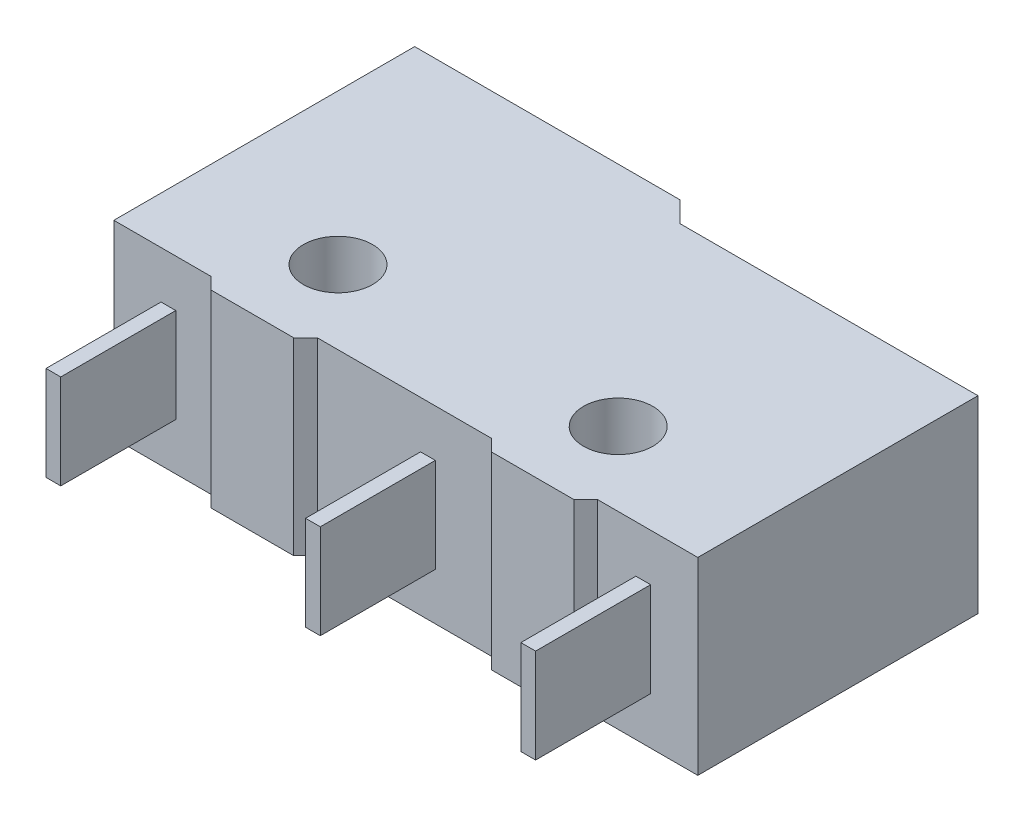
SolidWorks part; units mm, degrees
ref_plane "Front Plane" through (0, 0, 0) normal (0, 0, 1) x (1, 0, 0)
ref_plane "Top Plane" through (0, 0, 0) normal (0, 1, 0) x (1, 0, 0)
ref_plane "Right Plane" through (0, 0, 0) normal (1, 0, 0) x (0, 0, -1)
sketch "Sketch2" plane through (0, 0, 0) normal (0, 1, 0) x (1, 0, 0)
  line L0 (9.5, 0) -> (9.5, -2.5) construction
  line L1 (9.5, -2.5) -> (14.7, -2.5) construction
  line L2 (0, 0) -> (0, -2.5) construction
  line L3 (0, -2.5) -> (-5.1, -2.5) construction
  line L4 (0, 0) -> (0, -2.9) construction
  line L5 (0, -2.9) -> (-1.4, -2.9)
  line L6 (0, -2.9) -> (1.4, -2.9)
  line L7 (9.5, 0) -> (9.5, -2.9) construction
  line L8 (9.5, -2.9) -> (10.9, -2.9)
  line L9 (9.5, -2.9) -> (8.1, -2.9)
  line L10 (-1.4, -2.9) -> (-1.8, -2.5)
  line L11 (1.4, -2.9) -> (1.8, -2.5)
  line L12 (8.1, -2.9) -> (7.7, -2.5)
  line L13 (7.7, -2.5) -> (1.8, -2.5)
  line L14 (10.9, -2.9) -> (11.3, -2.5)
  line L15 (11.3, -2.5) -> (14.7, -2.5)
  line L16 (-1.8, -2.5) -> (-5.1, -2.5)
  line L17 (14.7, -2.5) -> (14.7, 7)
  line L18 (-5.1, -2.5) -> (-5.1, 7.7)
  line L19 (-5.1, 7.7) -> (3.9, 7.7)
  line L20 (3.9, 7.7) -> (4.6, 7)
  line L21 (4.6, 7) -> (14.7, 7)
  circle A0 centre (0, 0) radius 1.175
  circle A1 centre (9.5, 0) radius 1.175
  dimension "D1" = 2.35
  dimension "D2" = 2.35
  dimension "D3" = 9.5
  dimension "D4" = 5.2
  dimension "D5" = 2.5
  dimension "D6" = 2.5
  dimension "D7" = 5.1
  dimension "D8" = 2.9
  dimension "D9" = 1.4
  dimension "D10" = 1.4
  dimension "D11" = 1.4
  dimension "D12" = 1.4
  dimension "D13" = 2.9
  dimension "D14" = 135
  dimension "D15" = 135
  dimension "D16" = 135
  dimension "D17" = 135
  dimension "D18" = 9.5
  dimension "D19" = 10.2
  dimension "D20" = 9
  dimension "D21" = 10.1
extrude "Boss-Extrude1" add sketch "Sketch2" along normal blind 6.4
ref_plane "Plane1" through (0, 3.2, 0) normal (0, 1, 0) x (1, 0, 0)
sketch "Sketch3" plane through (0, 3.2, 0) normal (0, 1, 0) x (1, 0, 0)
  line L0 (3.9, 7.7) -> (3, 7.7) construction
  line L1 (3, 7.7) -> (1, 7.7)
  line L2 (2, 7.7) -> (2, 8.5382) construction
  line L3 (1, 7.7) -> (1, 7.954)
  line L4 (3, 7.7) -> (3, 7.954)
  spline S0 degree 2 poles (1, 7.954) (2, 9.1224) (3, 7.954) knots 0 0 0 1 1 1
  dimension "D1" = 2
  dimension "D2" = 0.9
  dimension "D3" = 0.8382
  dimension "D4" = 0.254
  dimension "D5" = 0.254
extrude "Boss-Extrude2" add sketch "Sketch3" along normal blind 1.6 and the other way blind 1.6
sketch "Sketch4" plane through (0, 3.2, 0) normal (0, 1, 0) x (1, 0, 0)
  line L0 (-5.1, -2.5) -> (-3.5, -2.5) construction
  line L1 (-3.5, -2.5) -> (-3, -2.5)
  line L2 (-3.5, -2.5) -> (-3.5, -6.4)
  line L3 (-3.5, -6.4) -> (-3, -6.4)
  line L4 (-3, -2.5) -> (-3, -6.4)
  line L5 (5.3, -2.5) -> (5.8, -2.5)
  line L6 (5.3, -2.5) -> (5.3, -6.4)
  line L7 (5.3, -6.4) -> (5.8, -6.4)
  line L8 (5.8, -2.5) -> (5.8, -6.4)
  line L9 (12.6, -2.5) -> (13.1, -2.5)
  line L10 (12.6, -2.5) -> (12.6, -6.4)
  line L11 (12.6, -6.4) -> (13.1, -6.4)
  line L12 (13.1, -2.5) -> (13.1, -6.4)
  line L13 (1.8, -2.5) -> (5.3, -2.5) construction
  line L14 (12.6, -2.5) -> (11.3, -2.5) construction
  point P20 (11.3, -2.5)
  dimension "D1" = 0.5
  dimension "D2" = 0.5
  dimension "D3" = 0.5
  dimension "D4" = 3.9
  dimension "D5" = 3.9
  dimension "D6" = 3.9
  dimension "D7" = 1.6
  dimension "D8" = 3.5
  dimension "D9" = 1.3
extrude "Boss-Extrude3" add sketch "Sketch4" along normal blind 1.6 and the other way blind 1.6
